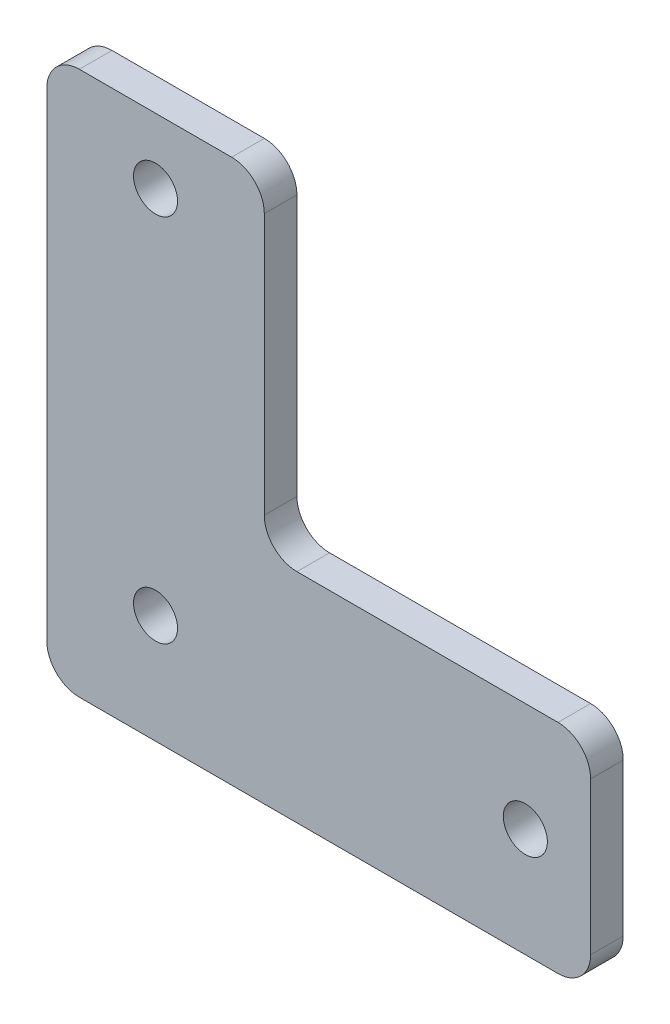
SolidWorks part; units mm, degrees
material "环氧玻璃布层压板"
ref_plane "前视基准面" through (0, 0, 0) normal (0, 0, 1) x (1, 0, 0)
ref_plane "上视基准面" through (0, 0, 0) normal (0, 1, 0) x (1, 0, 0)
ref_plane "右视基准面" through (0, 0, 0) normal (1, 0, 0) x (0, 0, -1)
sketch "草图1" plane through (0, 0, 0) normal (0, 0, 1) x (1, 0, 0)
  line L0 (0, 0) -> (0, 50)
  line L1 (0, 50) -> (20, 50)
  line L2 (20, 50) -> (20, 20)
  line L3 (20, 20) -> (50, 20)
  line L4 (50, 20) -> (50, 0)
  line L5 (50, 0) -> (0, 0)
  dimension "D1" = 20
  dimension "D2" = 20
  dimension "D3" = 50
extrude "凸台-拉伸1" add sketch "草图1" along normal blind 3
sketch "草图2" plane through (0, 0, 3) normal (0, 0, 1) x (1, 0, 0)
  line L0 (10, 50) -> (10, 10) construction
  line L1 (20, 50) -> (0, 50) construction
  line L2 (10, 10) -> (50, 10) construction
  line L3 (50, 0) -> (50, 20) construction
  circle A0 centre (10, 10) radius 2.025
  circle A1 centre (10, 44) radius 2.025
  circle A2 centre (44, 10) radius 2.025
  dimension "D3" = 4.05
  dimension "D1" = 6
  dimension "D2" = 6
extrude "切除-拉伸1" cut sketch "草图2" against normal blind 3
fillet "圆角1" radius 3 6 edges at (0, 0, 1.5) (0, 50, 1.5) (20, 50, 1.5) (20, 20, 1.5) (50, 0, 1.5) (50, 20, 1.5)
equation "\"D2@草图2\"=\"D1@草图2\""
